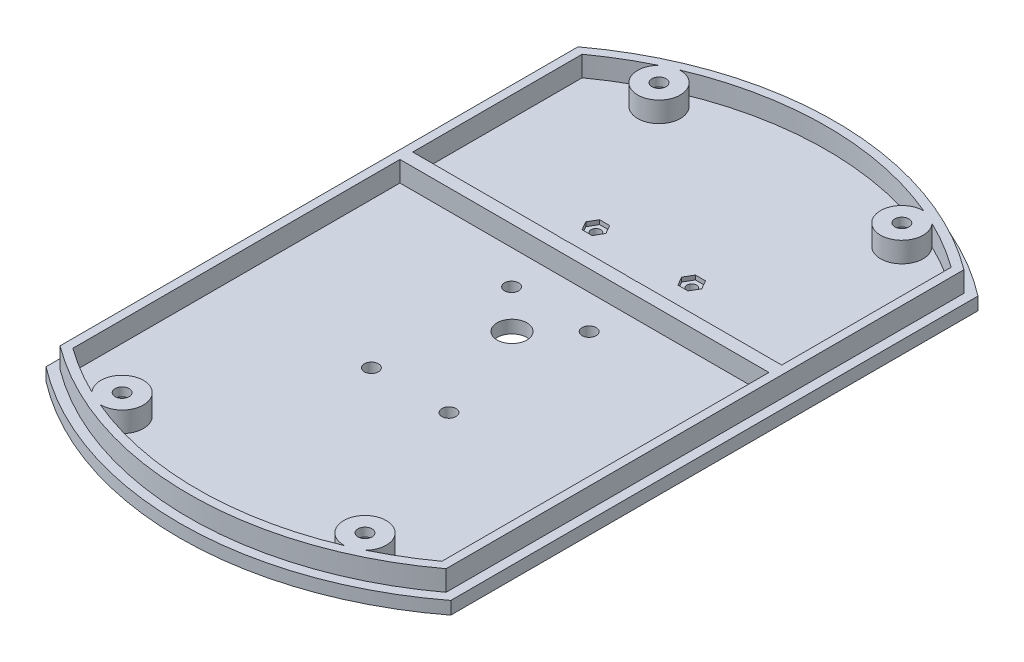
SolidWorks part; units mm, degrees
ref_plane "前视基准面" through (0, 0, 0) normal (0, 0, 1) x (1, 0, 0)
ref_plane "上视基准面" through (0, 0, 0) normal (0, 1, 0) x (1, 0, 0)
ref_plane "右视基准面" through (0, 0, 0) normal (1, 0, 0) x (0, 0, -1)
sketch "草图1" plane through (0, 0, 0) normal (0, 1, 0) x (1, 0, 0)
  line L2 (-47.5, 61.8688) -> (-47.5, -61.8688)
  line L4 (47.5, 61.8688) -> (47.5, -61.8688)
  line L5 (-28.5, -63) -> (28.5, -63) construction
  line L6 (-28.5, -63) -> (-28.5, 63) construction
  line L7 (-28.5, 63) -> (28.5, 63) construction
  line L8 (28.5, -63) -> (28.5, 63) construction
  line L9 (-28.5, -63) -> (28.5, 63) construction
  line L10 (-28.5, 63) -> (28.5, -63) construction
  arc A0 (-47.5, -61.8688) -> (47.5, -61.8688) centre (0, 0) ccw
  arc A1 (47.5, 61.8688) -> (-47.5, 61.8688) centre (0, 0) ccw
  circle A2 centre (-28.5, 63) radius 1.65
  circle A3 centre (28.5, 63) radius 1.65
  circle A4 centre (28.5, -63) radius 1.65
  circle A5 centre (-28.5, -63) radius 1.65
  point P1 (-47.5, 0)
  point P8 (0, 78)
  dimension "D2" = 78
  dimension "D3" = 3.3
  dimension "D1" = 95
  dimension "D4" = 57
  dimension "D5" = 126
extrude "凸台-拉伸1" add sketch "草图1" along normal blind 3
sketch "草图2" plane through (0, 3, 0) normal (0, 1, 0) x (1, 0, 0)
  line L2 (-43.3, 59.7624) -> (-43.3, -59.7624)
  line L3 (43.3, -59.7624) -> (43.3, 59.7624)
  line L4 (-45.3, 60.7746) -> (-45.3, -60.7746)
  line L5 (45.3, -60.7746) -> (45.3, 60.7746)
  line L6 (-45.3, 60.7746) -> (-45.3, -60.7746)
  line L7 (45.3, -60.7746) -> (45.3, 60.7746)
  arc A2 (43.3, 59.7624) -> (32.1296, 66.4389) centre (0, 0) ccw
  arc A3 (-43.3, -59.7624) -> (-32.1296, -66.4389) centre (0, 0) ccw
  arc A4 (45.3, 60.7746) -> (-45.3, 60.7746) centre (0, 0) ccw
  arc A5 (-45.3, -60.7746) -> (45.3, -60.7746) centre (0, 0) ccw
  arc A6 (45.3, 60.7746) -> (-45.3, 60.7746) centre (0, 0) ccw
  arc A7 (-45.3, -60.7746) -> (45.3, -60.7746) centre (0, 0) ccw
  arc A8 (-32.1296, 66.4389) -> (-28.6865, 67.9965) centre (-28.5, 63) ccw
  arc A9 (28.6865, 67.9965) -> (32.1296, 66.4389) centre (28.5, 63) ccw
  arc A10 (-28.6865, -67.9965) -> (-32.1296, -66.4389) centre (-28.5, -63) ccw
  arc A11 (32.1296, -66.4389) -> (28.6865, -67.9965) centre (28.5, -63) ccw
  arc A12 (-32.1296, 66.4389) -> (-43.3, 59.7624) centre (0, 0) ccw
  arc A13 (28.6865, 67.9965) -> (-28.6865, 67.9965) centre (0, 0) ccw
  arc A14 (43.3, 59.7624) -> (-43.3, 59.7624) centre (0, 0) ccw construction
  arc A15 (32.1296, -66.4389) -> (43.3, -59.7624) centre (0, 0) ccw
  arc A16 (-28.6865, -67.9965) -> (28.6865, -67.9965) centre (0, 0) ccw
  arc A17 (-43.3, -59.7624) -> (43.3, -59.7624) centre (0, 0) ccw construction
  circle A18 centre (-28.5, -63) radius 1.65 construction
  circle A19 centre (28.5, -63) radius 1.65 construction
  circle A20 centre (28.5, 63) radius 1.65 construction
  circle A21 centre (-28.5, 63) radius 1.65 construction
  circle A22 centre (-28.5, -63) radius 1.65
  circle A23 centre (28.5, -63) radius 1.65
  circle A24 centre (28.5, 63) radius 1.65
  circle A25 centre (-28.5, 63) radius 1.65
  dimension "D3" = 10
  dimension "D1" = 2.2
  dimension "D2" = 2
extrude "凸台-拉伸2" add sketch "草图2" along normal blind 4.8
sketch "草图7" plane through (0, 3, 0) normal (0, 1, 0) x (1, 0, 0)
  line L0 (-9.1, 9) -> (9.1, 9) construction
  line L1 (-9.1, 9) -> (-9.1, -23.9) construction
  line L2 (-9.1, -23.9) -> (9.1, -23.9) construction
  line L3 (9.1, 9) -> (9.1, -23.9) construction
  line L4 (-16, 14.87) -> (16, 14.87) construction
  line L5 (-16, 14.87) -> (-16, -31.13) construction
  line L6 (-16, -31.13) -> (16, -31.13) construction
  line L7 (16, 14.87) -> (16, -31.13) construction
  circle A0 centre (0, 0) radius 3.5
  circle A1 centre (9.1, 9) radius 1.65
  circle A2 centre (-9.1, 9) radius 1.65
  circle A3 centre (-9.1, -23.9) radius 1.65
  circle A4 centre (9.1, -23.9) radius 1.65
  point P6 (0, 14.87)
  point P7 (0, 9)
  dimension "D3" = 7
  dimension "D8" = 3.3
  dimension "D1" = 32.9
  dimension "D2" = 18.2
  dimension "D4" = 32
  dimension "D5" = 46
  dimension "D6" = 7.23
  dimension "D7" = 9
extrude "切除-拉伸1" cut sketch "草图7" against normal through all
sketch "草图8" plane through (0, 0, 0) normal (0, -1, 0) x (1, 0, 0)
  circle A0 centre (-28.5, -63) radius 1.65 construction
  circle A1 centre (28.5, -63) radius 1.65 construction
  circle A2 centre (28.5, 63) radius 1.65 construction
  circle A3 centre (-28.5, 63) radius 1.65 construction
  circle A8 centre (-28.5, -63) radius 1.65 construction
  circle A9 centre (28.5, -63) radius 1.65 construction
  circle A10 centre (28.5, 63) radius 1.65 construction
  circle A11 centre (-28.5, 63) radius 1.65 construction
  circle A12 centre (-28.5, -63) radius 3.25
  circle A13 centre (28.5, -63) radius 3.25
  circle A14 centre (28.5, 63) radius 3.25
  circle A15 centre (-28.5, 63) radius 3.25
  dimension "D1" = 1.6
extrude "切除-拉伸2" cut sketch "草图8" against normal offset from surface (5.8 mm away) 2 up to face at (0, 7.8, 0)
sketch "草图9" plane through (0, 3, 0) normal (0, 1, 0) x (1, 0, 0)
  line L0 (-43.3, 59.7624) -> (-43.3, -59.7624) construction
  line L1 (-43.3, 20) -> (43.3, 20)
  line L2 (-43.3, 20) -> (-43.3, 17)
  line L3 (-43.3, 17) -> (43.3, 17)
  line L4 (43.3, 20) -> (43.3, 17)
  line L5 (43.3, -59.7624) -> (43.3, 59.7624) construction
  circle A0 centre (0, 0) radius 3.5 construction
  dimension "D2" = 17
  dimension "D1" = 3
extrude "凸台-拉伸3" add sketch "草图9" along normal up to surface (4.8 mm away) up to face at (0, 7.8, 0)
sketch "草图10" plane through (0, 0, 0) normal (0, -1, 0) x (1, 0, 0)
  line L0 (7.719, -12.8615) -> (19.0402, -31.7249)
  line L1 (-7.719, -12.8615) -> (-19.0402, -31.7249)
  arc A0 (7.719, -12.8615) -> (-7.719, -12.8615) centre (0, 0) cw
  arc A1 (-19.0402, -31.7249) -> (19.0402, -31.7249) centre (0, 0) ccw
  point P8 (0, -15)
  dimension "D1" = 22
  dimension "D2" = 15
  dimension "D3" = 40
sketch "草图11" plane through (0, 0, 0) normal (0, -1, 0) x (1, 0, 0)
  line L0 (-11.2492, -30.9271) -> (-8, -22) construction
  line L1 (0, 0) -> (0, 13.5923) construction
  line L2 (0, 0) -> (-36.5988, 0) construction
  circle A0 centre (-8, -22) radius 1.15
  circle A1 centre (-11.2492, -30.9271) radius 1.15
  circle A2 centre (11.2492, -30.9271) radius 1.15
  circle A3 centre (8, -22) radius 1.15
  dimension "D1" = 2.3
  dimension "D2" = 9.5
  dimension "D3" = 22
  dimension "D4" = 8
  dimension "D5" = 70
extrude "切除-拉伸3" cut sketch "草图11" against normal through all
sketch "草图12" plane through (0, 3, 0) normal (0, 1, 0) x (1, 0, 0)
  line L1 (-10.0656, 32.9771) -> (-12.4328, 32.9771)
  line L2 (-12.4328, 32.9771) -> (-13.6163, 30.9271)
  line L3 (-13.6163, 30.9271) -> (-12.4328, 28.8771)
  line L4 (-12.4328, 28.8771) -> (-10.0656, 28.8771)
  line L5 (-10.0656, 28.8771) -> (-8.8821, 30.9271)
  line L6 (-8.8821, 30.9271) -> (-10.0656, 32.9771)
  line L7 (-5.6329, 22) -> (-6.8164, 24.05)
  line L8 (-6.8164, 24.05) -> (-9.1836, 24.05)
  line L9 (-9.1836, 24.05) -> (-10.3671, 22)
  line L10 (-10.3671, 22) -> (-9.1836, 19.95)
  line L11 (-9.1836, 19.95) -> (-6.8164, 19.95)
  line L12 (-6.8164, 19.95) -> (-5.6329, 22)
  line L13 (10.3671, 22) -> (9.1836, 24.05)
  line L14 (9.1836, 24.05) -> (6.8164, 24.05)
  line L15 (6.8164, 24.05) -> (5.6329, 22)
  line L16 (5.6329, 22) -> (6.8164, 19.95)
  line L17 (6.8164, 19.95) -> (9.1836, 19.95)
  line L18 (9.1836, 19.95) -> (10.3671, 22)
  line L19 (12.4328, 32.9771) -> (10.0656, 32.9771)
  line L20 (10.0656, 32.9771) -> (8.8821, 30.9271)
  line L21 (8.8821, 30.9271) -> (10.0656, 28.8771)
  line L22 (10.0656, 28.8771) -> (12.4328, 28.8771)
  line L23 (12.4328, 28.8771) -> (13.6163, 30.9271)
  line L24 (13.6163, 30.9271) -> (12.4328, 32.9771)
  circle A0 centre (-11.2492, 30.9271) radius 2.05 construction
  circle A1 centre (-8, 22) radius 2.05 construction
  circle A2 centre (8, 22) radius 2.05 construction
  circle A3 centre (11.2492, 30.9271) radius 2.05 construction
  dimension "D1" = 4.1
extrude "切除-拉伸4" cut sketch "草图12" against normal offset from surface 2 and the other way through all up to face at (8, 0, -20.85)
